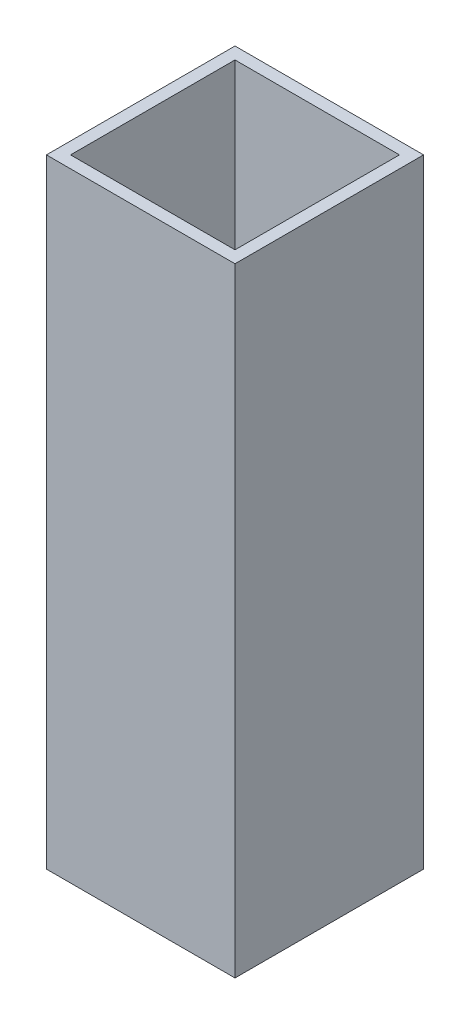
SolidWorks part; units mm, degrees
ref_plane "Front Plane" through (0, 0, 0) normal (0, 0, 1) x (1, 0, 0)
ref_plane "Top Plane" through (0, 0, 0) normal (0, 1, 0) x (1, 0, 0)
ref_plane "Right Plane" through (0, 0, 0) normal (1, 0, 0) x (0, 0, -1)
sketch "Sketch1" plane through (0, 0, 0) normal (0, 1, 0) x (1, 0, 0)
  line L1 (-4.786, 4.6453) -> (7.714, 4.6453)
  line L2 (-4.786, 4.6453) -> (-4.786, -7.8547)
  line L3 (-4.786, -7.8547) -> (7.714, -7.8547)
  line L4 (7.714, 4.6453) -> (7.714, -7.8547)
  dimension "D1" = 12.5
  dimension "D2" = 12.5
extrude "Boss-Extrude1" add sketch "Sketch1" along normal blind 41
shell "Shell1" thickness 0.8
